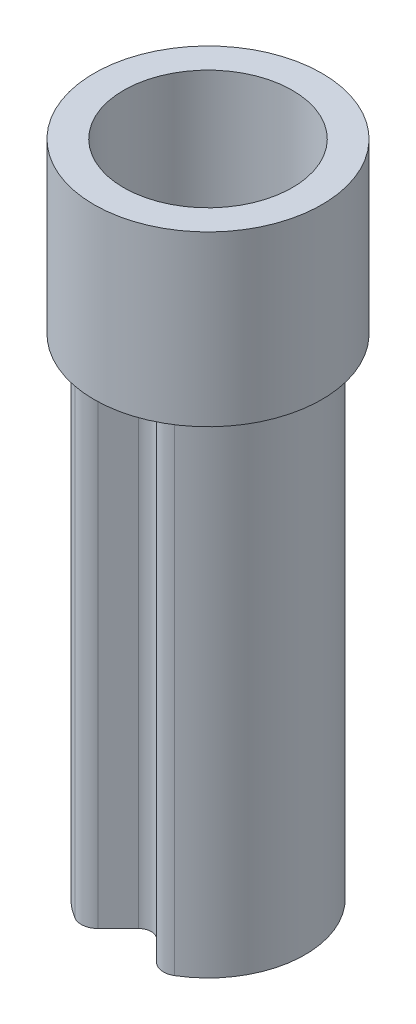
SolidWorks part; units mm, degrees
ref_plane "Front Plane" through (0, 0, 0) normal (0, 0, 1) x (1, 0, 0)
ref_plane "Top Plane" through (0, 0, 0) normal (0, 1, 0) x (1, 0, 0)
ref_plane "Right Plane" through (0, 0, 0) normal (1, 0, 0) x (0, 0, -1)
sketch "Sketch1" plane through (0, 0, 0) normal (0, 1, 0) x (1, 0, 0)
  line L0 (0, 0) -> (0, -1.15) construction
  line L1 (-0.4488, -1.0588) -> (-0.1061, -0.7161)
  line L2 (0.1061, -0.7161) -> (0.4488, -1.0588)
  line L3 (-0.4796, -0.8775) -> (-0.2121, -0.61)
  line L4 (0.2121, -0.61) -> (0.4796, -0.8775)
  arc A0 (0.4488, -1.0588) -> (-0.4488, -1.0588) centre (0, 0) ccw
  arc A1 (0.1061, -0.7161) -> (-0.1061, -0.7161) centre (0, -0.8221) ccw
  arc A2 (0.2121, -0.61) -> (-0.2121, -0.61) centre (0, -0.8221) ccw
  arc A3 (0.4796, -0.8775) -> (-0.4796, -0.8775) centre (0, 0) ccw
  point P8 (0, -0.61)
  dimension "D1" = 2.3
  dimension "D3" = 0.15
  dimension "D2" = 0.61
  dimension "D4" = 0.15
extrude "Boss-Extrude1" add sketch "Sketch1" along normal blind 5.8 contours A3 L3 A2 L4
fillet "Fillet1" radius 0.05 2 edges at (0.4796, 2.9, 0.8775) (-0.4796, 2.9, 0.8775)
fillet "Fillet2" radius 0.2 2 edges at (0.4488, 2.9, 1.0588) (-0.4488, 2.9, 1.0588)
sketch "Sketch2" plane through (0, 5.8, 0) normal (0, 1, 0) x (1, 0, 0)
  circle A0 centre (0, 0) radius 1.35
  circle A1 centre (0, 0) radius 1
  arc A2 (0.5136, -0.858) -> (-0.5136, -0.858) centre (0, 0) ccw construction
  dimension "D1" = 2.7
extrude "Boss-Extrude2" add sketch "Sketch2" along normal offset from surface (2 mm away) 7.8 up to face at (0, 0, 0.537)
